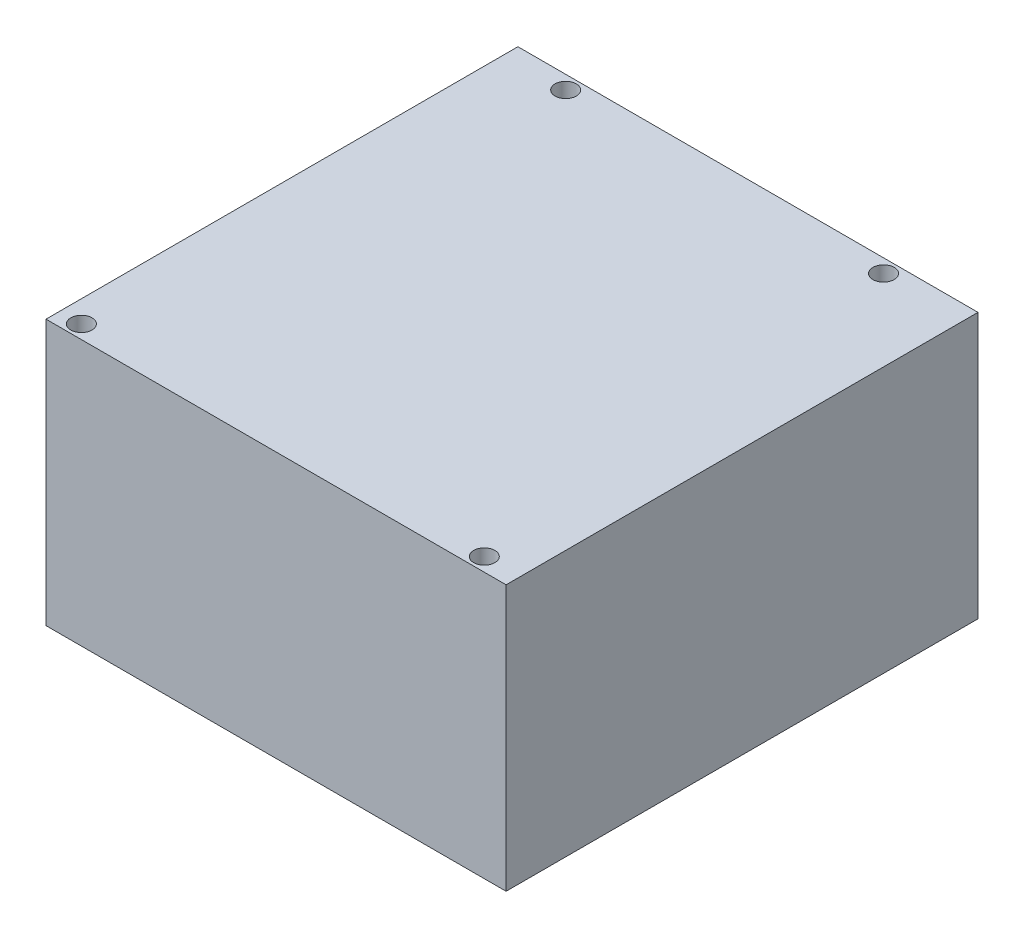
SolidWorks part; units mm, degrees
ref_plane "Front Plane" through (0, 0, 0) normal (0, 0, 1) x (1, 0, 0)
ref_plane "Top Plane" through (0, 0, 0) normal (0, 1, 0) x (1, 0, 0)
ref_plane "Right Plane" through (0, 0, 0) normal (1, 0, 0) x (0, 0, -1)
sketch "Sketch1" plane through (0, 0, 0) normal (0, 1, 0) x (1, 0, 0)
  line L1 (0, 0) -> (78, 0)
  line L2 (0, 0) -> (0, 80)
  line L3 (0, 80) -> (78, 80)
  line L4 (78, 0) -> (78, 80)
  dimension "D1" = 78
  dimension "D2" = 80
extrude "Boss-Extrude1" add sketch "Sketch1" along normal blind 45
sketch "Sketch2" plane through (0, 45, 0) normal (0, 1, 0) x (1, 0, 0)
  line L0 (10.4, 77.7) -> (64.29, 77.7) construction
  line L5 (0, 80) -> (0, 0) construction
  line L6 (78, 80) -> (0, 80) construction
  line L8 (0, 0) -> (78, 0) construction
  line L9 (78, 0) -> (78, 80) construction
  point P9 (72, 2.3)
  point P12 (3.7, 2.3)
  dimension "D1" = 2.3
  dimension "D2" = 53.89
  dimension "D3" = 10.4
  dimension "D4" = 2.3
  dimension "D5" = 3.7
  dimension "D6" = 6
  dimension "D7" = 2.3
  dimension "D8" = 13.71
hole_wizard "M3 Clearance Hole1" positions "Sketch3" profile "Sketch4" hole size "M3" standard "ANSI Metric" end condition up to next
sketch "Sketch3" plane through (0, 45, 0) normal (0, 1, 0) x (1, 0, 0)
  point P0 (10.4, 77.7)
  point P3 (64.29, 77.7)
  point P6 (72, 2.3)
  point P9 (3.7, 2.3)
sketch "Sketch4" plane through (10.4, 45, -77.7) normal (1, 0, 0) x (0, 0, 1)
  line L0 (0, 0) -> (0, 45)
  line L1 (0, 45) -> (1.8, 45)
  line L2 (1.8, 45) -> (1.8, 0)
  line L5 (1.8, 0) -> (0, 0)
  line L11 (0, -6.35) -> (0, 107.95) construction
  dimension "Thru Hole Dia." = 3.6
  dimension "Thru Hole Depth" = 45
